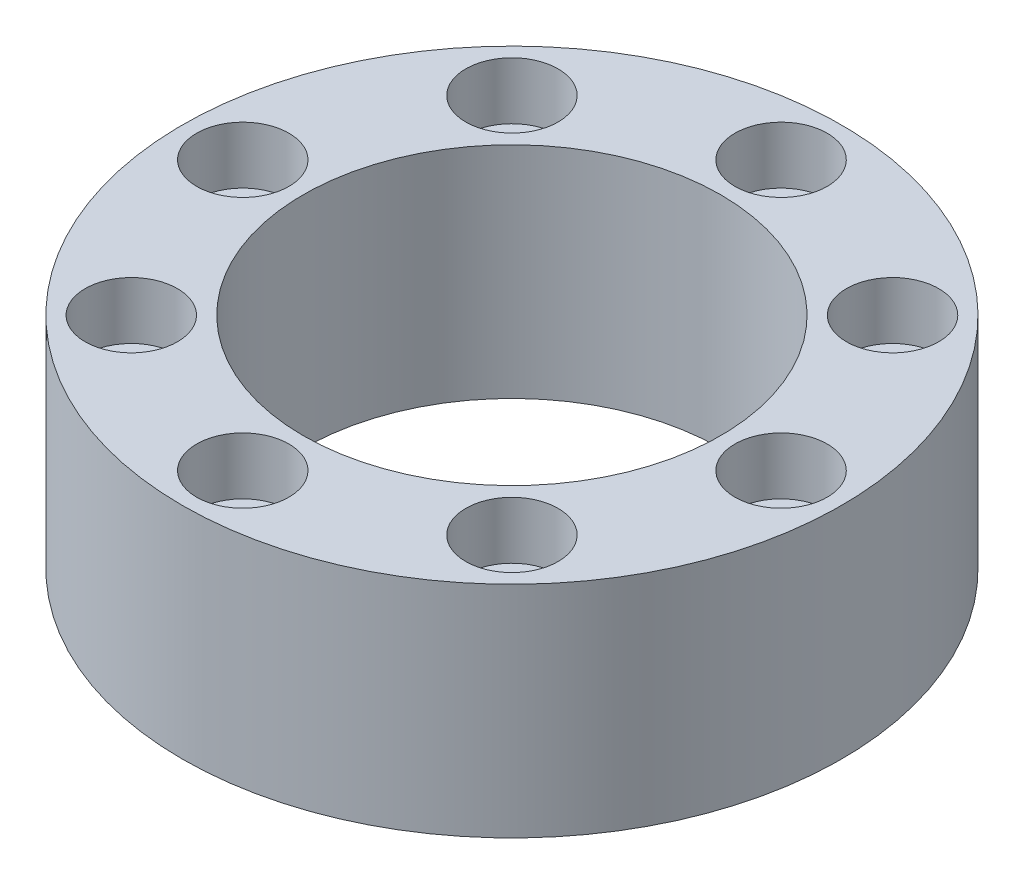
SolidWorks part; units mm, degrees
material "PVC rigide"
ref_plane "Plan de face" through (0, 0, 0) normal (0, 0, 1) x (1, 0, 0)
ref_plane "Plan de dessus" through (0, 0, 0) normal (0, 1, 0) x (1, 0, 0)
ref_plane "Plan de droite" through (0, 0, 0) normal (1, 0, 0) x (0, 0, -1)
sketch "Esquisse1" plane through (0, 0, 0) normal (0, 1, 0) x (1, 0, 0)
  circle A0 centre (0, 0) radius 19
  circle A1 centre (0, 0) radius 30
  dimension "D1" = 60
  dimension "D2" = 38
extrude "Boss.-Extru.2" add sketch "Esquisse1" along normal blind 20
sketch "Esquisse5" plane through (0, 20, 0) normal (0, 1, 0) x (1, 0, 0)
  line L0 (0, 0) -> (30, 0) construction
  circle A0 centre (0, 0) radius 30 construction
  circle A1 centre (0, 0) radius 24.5 construction
  circle A2 centre (24.5, 0) radius 2.55
  circle A3 centre (17.3241, -17.3241) radius 2.55
  circle A4 centre (0, -24.5) radius 2.55
  circle A5 centre (-17.3241, -17.3241) radius 2.55
  circle A6 centre (-24.5, 0) radius 2.55
  circle A7 centre (-17.3241, 17.3241) radius 2.55
  circle A8 centre (0, 24.5) radius 2.55
  circle A9 centre (17.3241, 17.3241) radius 2.55
  dimension "D1" = 49
  dimension "D2" = 5.1
  dimension "D3" = 8
extrude "Enlèv. mat.-Extru.3" cut sketch "Esquisse5" against normal through all
sketch "Esquisse6" plane through (0, 20, 0) normal (0, 1, 0) x (1, 0, 0)
  circle A0 centre (24.5, 0) radius 4.2
  circle A1 centre (0, 0) radius 24.5 construction
  circle A2 centre (17.3241, 17.3241) radius 4.2
  circle A3 centre (0, 24.5) radius 4.2
  circle A4 centre (-17.3241, 17.3241) radius 4.2
  circle A5 centre (-24.5, 0) radius 4.2
  circle A6 centre (-17.3241, -17.3241) radius 4.2
  circle A7 centre (0, -24.5) radius 4.2
  circle A8 centre (17.3241, -17.3241) radius 4.2
  dimension "D1" = 8.4
  dimension "D2" = 8
extrude "Enlèv. mat.-Extru.4" cut sketch "Esquisse6" against normal blind 5.2
